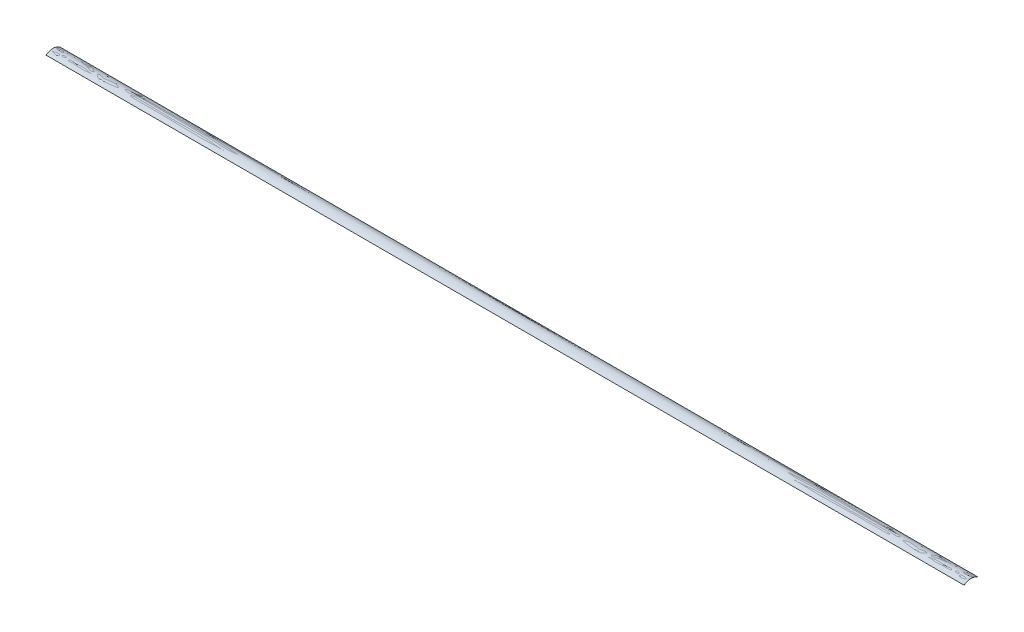
SolidWorks part; units mm, degrees
ref_plane "Front" through (0, 0, 0) normal (0, 0, 1) x (1, 0, 0)
ref_plane "Top" through (0, 0, 0) normal (0, 1, 0) x (1, 0, 0)
ref_plane "Right" through (0, 0, 0) normal (1, 0, 0) x (0, 0, -1)
sketch "Sketch1" plane through (0, 0, 0) normal (1, 0, 0) x (0, 0, -1)
  line L0 (7.55, 0) -> (7.45, 0)
  line L1 (-7.45, 0) -> (-7.55, 0)
  spline S0 degree 2 poles (7.55, 0) (0, 5.1) (-7.55, 0) knots 0 0 0 1 1 1
  spline S1 degree 2 poles (-7.45, 0) (0, 4.9) (7.45, 0) knots 0 0 0 1 1 1
  dimension "D6" = 2.45
  dimension "D1" = 7.55
  dimension "D2" = 7.55
  dimension "D3" = 2.55
  dimension "D4" = 7.45
  dimension "D5" = 7.45
  dimension "D7" = 0
  dimension "D8" = 0
  dimension "D9" = 0
extrude "Boss-Extrude1" add sketch "Sketch1" along normal mid plane 990.6
